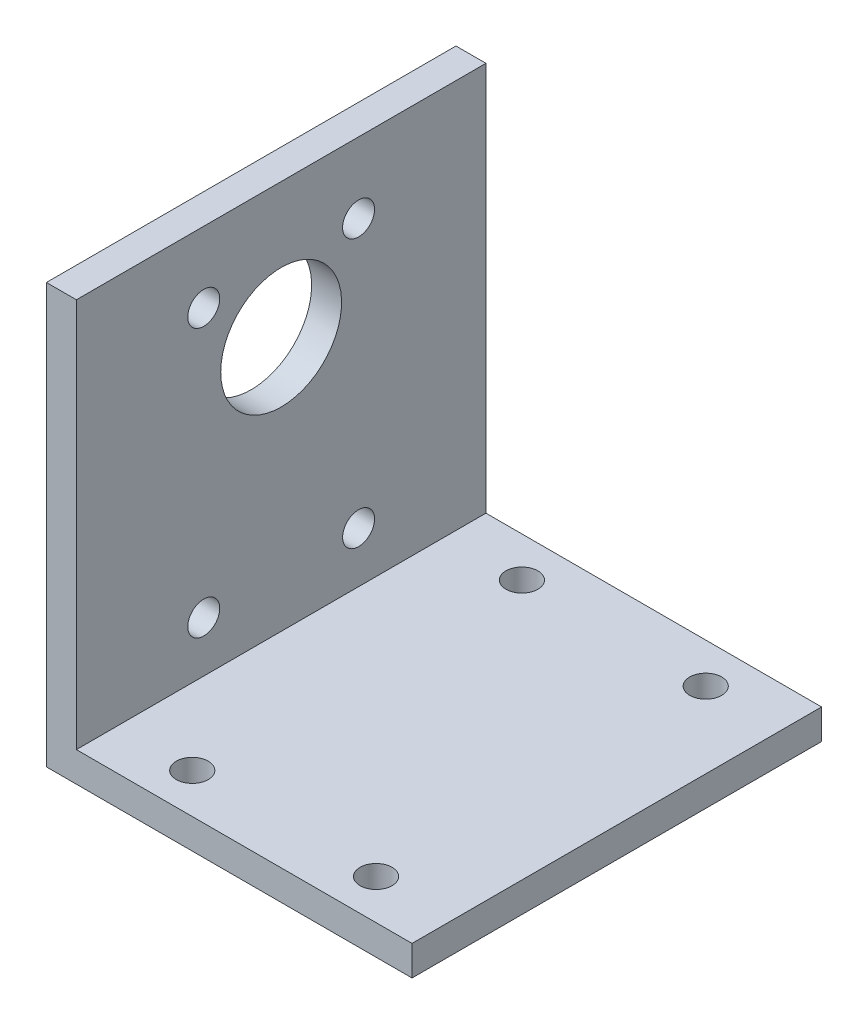
SolidWorks part; units mm, degrees
ref_plane "正面" through (0, 0, 0) normal (0, 0, 1) x (1, 0, 0)
ref_plane "平面" through (0, 0, 0) normal (0, 1, 0) x (1, 0, 0)
ref_plane "右側面" through (0, 0, 0) normal (1, 0, 0) x (0, 0, -1)
sketch "ｽｹｯﾁ1" plane through (0, 0, 0) normal (0, 0, 1) x (1, 0, 0)
  line L0 (0, 0) -> (0, 42)
  line L1 (0, 42) -> (3, 42)
  line L2 (3, 42) -> (3, 3)
  line L3 (3, 3) -> (36.6, 3)
  line L4 (36.6, 3) -> (36.6, 0)
  line L5 (36.6, 0) -> (0, 0)
  dimension "D1" = 42
  dimension "D2" = 36.6
  dimension "D3" = 3
  dimension "D4" = 3
extrude "ﾎﾞｽ - 押し出し1" add sketch "ｽｹｯﾁ1" along normal blind 41
sketch "ｽｹｯﾁ2" plane through (0, 0, 0) normal (-1, 0, 0) x (0, 0, 1)
  line L0 (20.5, 42) -> (20.5, 28.5)
  line L1 (41, 42) -> (0, 42) construction
  line L2 (20.5, 28.5) -> (28.25, 28.5)
  line L3 (28.25, 28.5) -> (28.25, 34.925)
  line L4 (20.5, 28.5) -> (12.75, 28.5)
  line L5 (12.75, 28.5) -> (12.75, 34.925)
  line L6 (12.75, 34.925) -> (12.75, 8.075)
  line L7 (28.25, 34.925) -> (28.25, 8.075)
  circle A0 centre (20.5, 28.5) radius 6.05
  circle A1 centre (28.25, 34.925) radius 1.6
  circle A2 centre (12.75, 34.925) radius 1.6
  circle A3 centre (12.75, 8.075) radius 1.6
  circle A4 centre (28.25, 8.075) radius 1.6
  dimension "D5" = 3.2
  dimension "D6" = 3.2
  dimension "D8" = 12.1
  dimension "D11" = 3.2
  dimension "D12" = 3.2
  dimension "D1" = 13.5
  dimension "D2" = 7.75
  dimension "D3" = 6.425
  dimension "D4" = 7.75
  dimension "D7" = 6.425
  dimension "D9" = 26.85
  dimension "D10" = 26.85
extrude "ｶｯﾄ - 押し出し1" cut sketch "ｽｹｯﾁ2" against normal blind 41
sketch "ｽｹｯﾁ3" plane through (0, 0, 0) normal (0, -1, 0) x (-1, 0, 0)
  line L0 (0, -20.5) -> (0, -37)
  line L1 (0, -41) -> (0, 0) construction
  line L2 (0, -37) -> (-10.6, -37)
  line L3 (0, -20.5) -> (0, -4)
  line L4 (0, -4) -> (-10.6, -4)
  line L5 (-10.6, -4) -> (-29, -4)
  line L6 (-10.6, -37) -> (-29, -37)
  circle A0 centre (-10.6, -37) radius 1.6
  circle A1 centre (-10.6, -4) radius 1.6
  circle A2 centre (-29, -4) radius 1.6
  circle A3 centre (-29, -37) radius 1.6
  point P13 (0, 0)
  dimension "D3" = 3.2
  dimension "D6" = 3.2
  dimension "D9" = 3.2
  dimension "D10" = 3.2
  dimension "D1" = 16.5
  dimension "D2" = 16.5
  dimension "D4" = 10.6
  dimension "D5" = 10.6
  dimension "D7" = 18.4
  dimension "D8" = 18.4
extrude "ｶｯﾄ - 押し出し2" cut sketch "ｽｹｯﾁ3" against normal blind 41
